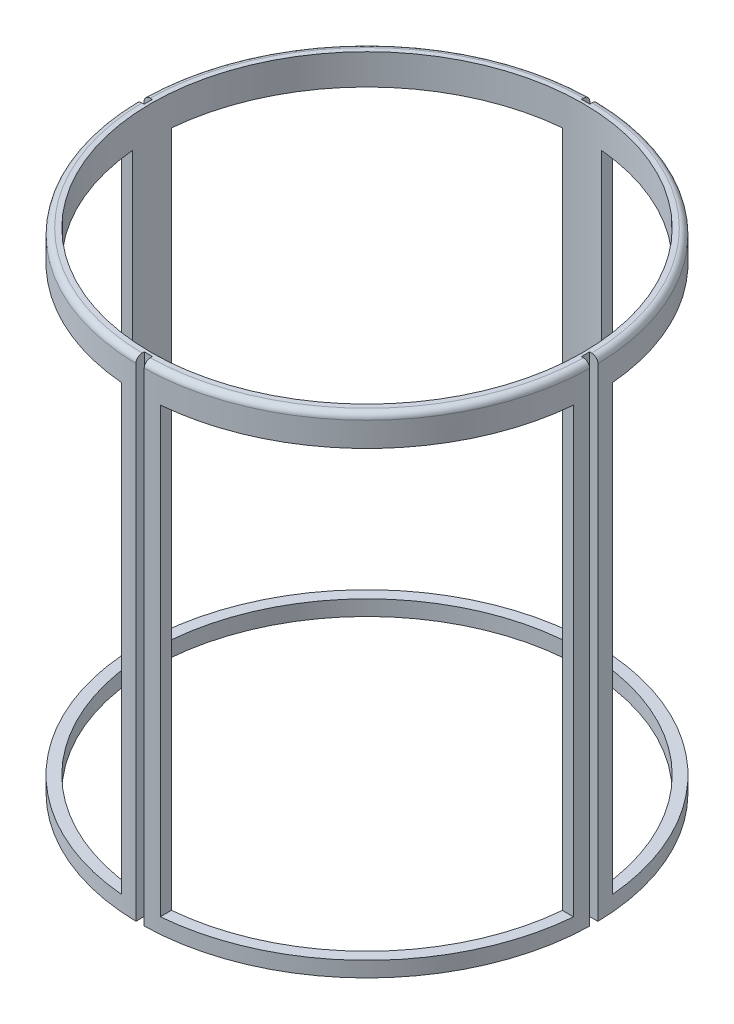
SolidWorks part; units mm, degrees
ref_plane "Front" through (0, 0, 0) normal (0, 0, 1) x (1, 0, 0)
ref_plane "Top" through (0, 0, 0) normal (0, 1, 0) x (1, 0, 0)
ref_plane "Right" through (0, 0, 0) normal (1, 0, 0) x (0, 0, -1)
sketch "Sketch1" plane through (0, 0, 0) normal (0, 1, 0) x (1, 0, 0)
  circle A0 centre (0, 0) radius 89.662
  circle A1 centre (0, 0) radius 94.2975
  dimension "Inner Diameter" = 179.324
  dimension "Outer Diameter" = 188.595
extrude "Boss-Extrude1" add sketch "Sketch1" against normal blind 203.2
sketch "Sketch5" plane through (0, 0, 0) normal (0, 1, 0) x (1, 0, 0)
  line L0 (0, 114.2751) -> (0, -136.7211) construction
  line L1 (-124.857, 0) -> (116.4345, 0) construction
  line L2 (-1.7145, 90.8209) -> (1.7145, 90.8209)
  line L3 (1.7145, 90.8209) -> (1.7145, 95.9009)
  line L4 (1.7145, 95.9009) -> (-1.7145, 95.9009)
  line L5 (-1.7145, 95.9009) -> (-1.7145, 90.8209)
  line L6 (1.7145, -95.9009) -> (-1.7145, -95.9009)
  line L7 (1.7145, -90.8209) -> (1.7145, -95.9009)
  line L8 (-1.7145, -90.8209) -> (1.7145, -90.8209)
  line L9 (-1.7145, -95.9009) -> (-1.7145, -90.8209)
  line L10 (-90.8209, 1.651) -> (-90.8209, -1.778)
  line L11 (-90.8209, -1.778) -> (-95.9009, -1.778)
  line L12 (-95.9009, -1.778) -> (-95.9009, 1.651)
  line L13 (-95.9009, 1.651) -> (-90.8209, 1.651)
  line L14 (95.9009, -1.778) -> (95.9009, 1.651)
  line L15 (90.8209, -1.778) -> (95.9009, -1.778)
  line L16 (90.8209, 1.651) -> (90.8209, -1.778)
  line L17 (95.9009, 1.651) -> (90.8209, 1.651)
  dimension "D1" = 1.7145
  dimension "D2" = 1.7145
  dimension "D3" = 5.08
  dimension "D4" = 90.8209
  dimension "D5" = 1.651
  dimension "D6" = 90.8209
extrude "Cut-Extrude1" cut sketch "Sketch5" against normal blind 203.2
sketch "Sketch7" plane through (0, 0, 0) normal (0, 1, 0) x (1, 0, 0)
  line L0 (89.2928, -8.128) -> (93.9465, -8.128)
  line L1 (8.0645, -89.2986) -> (8.0645, -93.952)
  line L2 (1.7145, -94.2819) -> (1.7145, -90.8209) construction
  line L3 (90.8209, -1.778) -> (94.2807, -1.778) construction
  arc A0 (89.2928, -8.128) -> (8.0645, -89.2986) centre (0, 0) cw
  circle A1 centre (0, 0) radius 89.662 construction
  arc A2 (93.9465, -8.128) -> (8.0645, -93.952) centre (0, 0) cw
  arc A3 (1.7145, -94.2819) -> (94.2807, -1.778) centre (0, 0) ccw construction
  point P15 (92.5508, -1.778)
  dimension "D3" = 94.2975
  dimension "D4" = 89.662
  dimension "D1" = 6.35
  dimension "D2" = 6.35
extrude "Cut-Extrude2" cut sketch "Sketch7" against normal blind 184.15 from offset 12.7 offset against normal yes
pattern_circular "CirPattern1" count 4 over 360 about axis through (0, 0, 0) along (0, 1, 0) of "Cut-Extrude2"
fillet "Fillet1" radius 2.54 4 edges at (-66.7009, 0, -66.6559) (66.7009, 0, -66.6559) (66.6559, 0, 66.7009) (-66.6559, 0, 66.7009)
equation "\"D4@Sketch5\"=(\"Inner Diameter\"/2)+((\"Outer Diameter\"-\"Inner Diameter\")/8)"
equation "\"D6@Sketch5\"=(\"Inner Diameter\"/2)+((\"Outer Diameter\"-\"Inner Diameter\")/8)"
equation "\"D1@Cut-Extrude1\"=\"Fin Length\""
equation "\"D3@Sketch7\"=\"Outer Diameter\"/2"
equation "\"D4@Sketch7\"=\"Inner Diameter\"/2"
